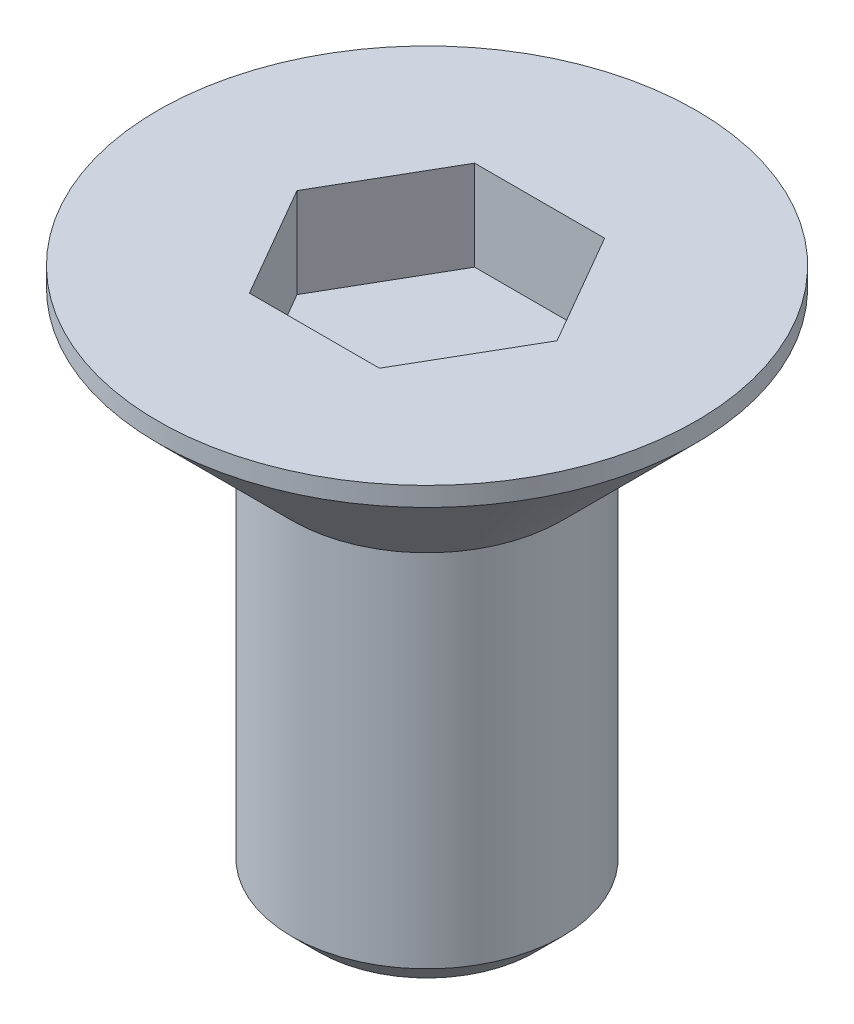
SolidWorks part; units mm, degrees
material "acero"
ref_plane "Alzado" through (0, 0, 0) normal (0, 0, 1) x (1, 0, 0)
ref_plane "Planta" through (0, 0, 0) normal (0, 1, 0) x (1, 0, 0)
ref_plane "Vista lateral" through (0, 0, 0) normal (1, 0, 0) x (0, 0, -1)
sketch "Croquis1" plane through (0, 0, 0) normal (0, 0, 1) x (1, 0, 0)
  line L0 (0, 0) -> (0, -60.9498) construction
  line L1 (0, 0) -> (3.2, 0)
  line L2 (1.5, -1.7) -> (3.2, 0)
  line L4 (1.5, -1.7) -> (1.5, -6)
  line L5 (1.5, -6) -> (0, -6)
  line L6 (0, -6) -> (0, 0)
  dimension "D1" = 6
  dimension "D2" = 45
  dimension "D3" = 1.7
  dimension "D4" = 3
revolve "Revolución1" add sketch "Croquis1" angle 360 about L0
chamfer "Chaflán2" distance 0.3 angle 45 1 edges at (0, 0, 3.2)
chamfer "Chaflán3" distance 0.3 angle 45 1 edges at (0, -6, 1.5)
sketch "Croquis3" plane through (0, 0, 0) normal (0, 1, 0) x (1, 0, 0)
  line L1 (-0.7217, 1.25) -> (-1.4434, 0)
  line L2 (-1.4434, 0) -> (-0.7217, -1.25)
  line L3 (-0.7217, -1.25) -> (0.7217, -1.25)
  line L4 (0.7217, -1.25) -> (1.4434, 0)
  line L5 (1.4434, 0) -> (0.7217, 1.25)
  line L6 (0.7217, 1.25) -> (-0.7217, 1.25)
  circle A0 centre (0, 0) radius 1.25 construction
  dimension "D1" = 2.5
extrude "Cortar-Extruir2" cut sketch "Croquis3" against normal blind 1
